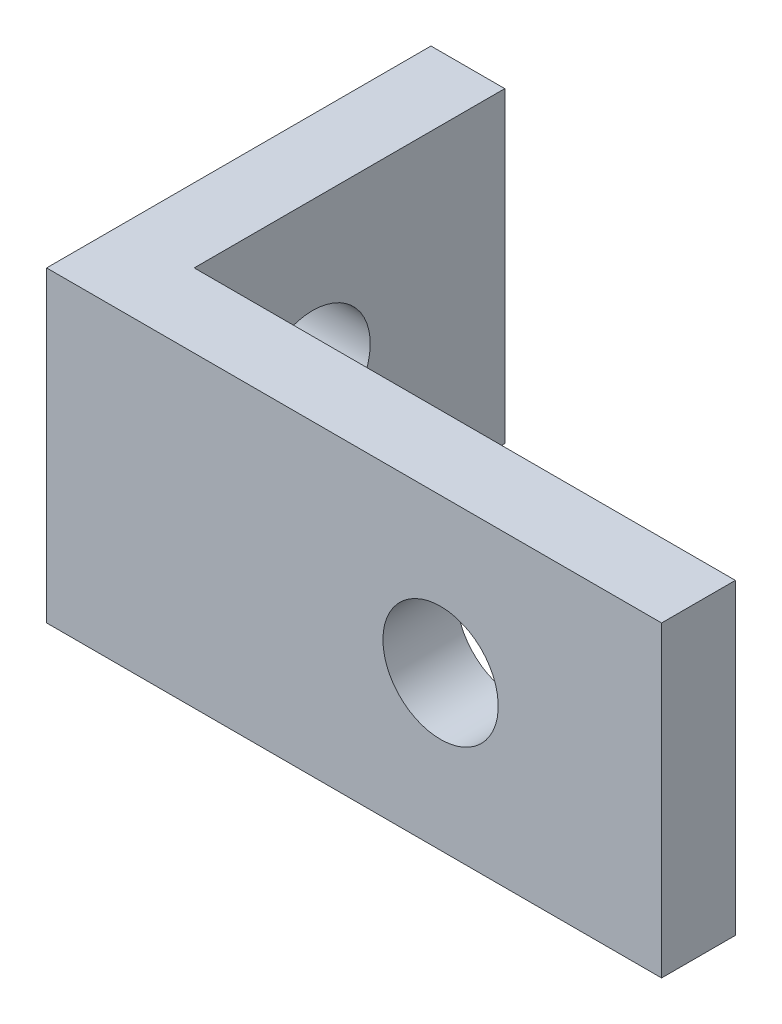
SolidWorks part; units mm, degrees
ref_plane "Front Plane" through (0, 0, 0) normal (0, 0, 1) x (1, 0, 0)
ref_plane "Top Plane" through (0, 0, 0) normal (0, 1, 0) x (1, 0, 0)
ref_plane "Right Plane" through (0, 0, 0) normal (1, 0, 0) x (0, 0, -1)
sketch "Sketch1" plane through (0, 0, 0) normal (0, 0, 1) x (1, 0, 0)
  line L1 (0, 0) -> (25.4, 0)
  line L2 (0, 0) -> (0, 12.7)
  line L3 (0, 12.7) -> (25.4, 12.7)
  line L4 (25.4, 0) -> (25.4, 12.7)
  dimension "D1" = 25.4
  dimension "D2" = 12.7
extrude "Boss-Extrude1" add sketch "Sketch1" along normal blind 3.048
sketch "Sketch2" plane through (0, 0, 3.048) normal (0, 0, 1) x (1, 0, 0)
  line L0 (25.4, 12.7) -> (0, 12.7) construction
  line L1 (0, 12.7) -> (3.048, 12.7)
  line L2 (0, 12.7) -> (0, 0)
  line L3 (0, 0) -> (3.048, 0)
  line L4 (3.048, 12.7) -> (3.048, 0)
  line L5 (0, 12.7) -> (0, 0) construction
  line L6 (0, 0) -> (25.4, 0) construction
  dimension "D1" = 3.048
extrude "Boss-Extrude2" add sketch "Sketch2" against normal blind 15.875
sketch "Sketch3" plane through (0, 0, 0) normal (0, 0, -1) x (-1, 0, 0)
  line L0 (-25.4, 6.35) -> (-16.2719, 6.35) construction
  line L1 (-25.4, 0) -> (-25.4, 12.7) construction
  circle A0 centre (-16.2719, 6.35) radius 2.3813
  dimension "D2" = 4.7625
  dimension "D1" = 9.1281
extrude "Cut-Extrude1" cut sketch "Sketch3" against normal through all
sketch "Sketch4" plane through (3.048, 0, 0) normal (1, 0, 0) x (0, 0, -1)
  line L0 (12.827, 6.35) -> (4.8895, 6.35) construction
  line L1 (12.827, 0) -> (12.827, 12.7) construction
  circle A0 centre (4.8895, 6.35) radius 2.3813
  dimension "D2" = 4.7625
  dimension "D1" = 7.9375
extrude "Cut-Extrude2" cut sketch "Sketch4" against normal through all
